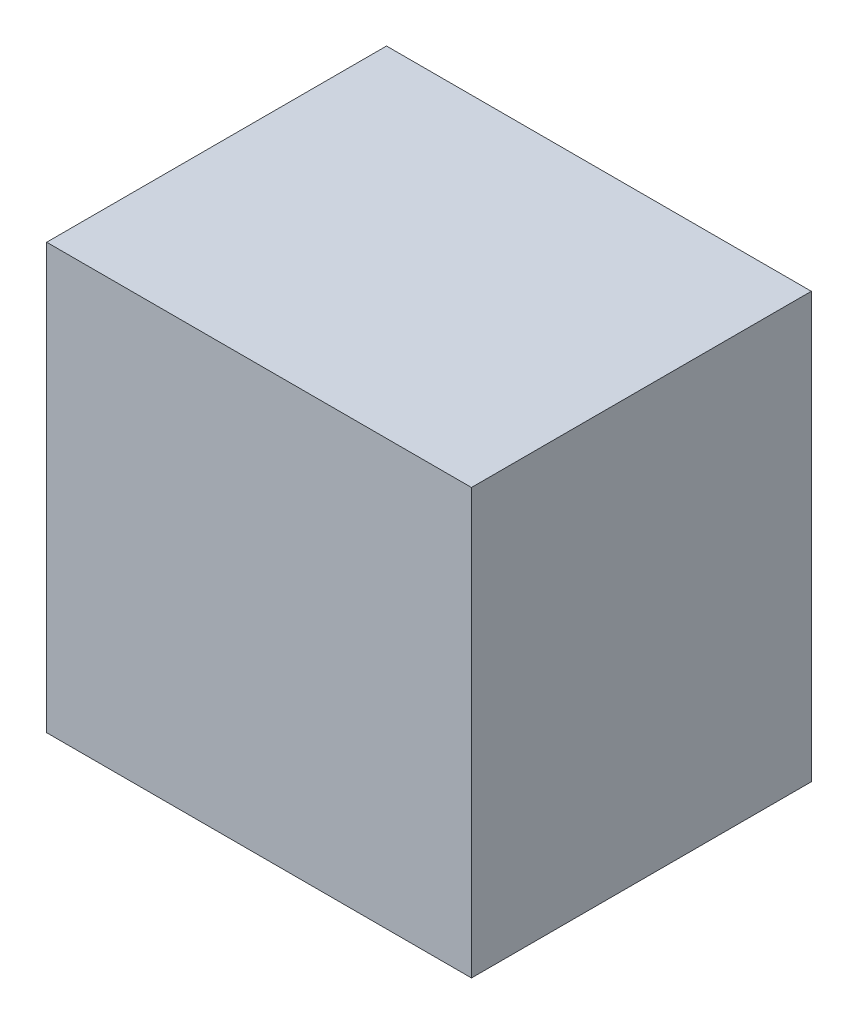
SolidWorks part; units mm, degrees
ref_plane "Front Plane" through (0, 0, 0) normal (0, 0, 1) x (1, 0, 0)
ref_plane "Top Plane" through (0, 0, 0) normal (0, 1, 0) x (1, 0, 0)
ref_plane "Right Plane" through (0, 0, 0) normal (1, 0, 0) x (0, 0, -1)
sketch "Sketch1" plane through (0, 0, 0) normal (0, 1, 0) x (1, 0, 0)
  line L1 (0, 0) -> (100, 0)
  line L2 (0, 0) -> (0, 80)
  line L3 (0, 80) -> (100, 80)
  line L4 (100, 0) -> (100, 80)
  dimension "D1" = 80
  dimension "D2" = 100
extrude "Boss-Extrude1" add sketch "Sketch1" along normal blind 100
